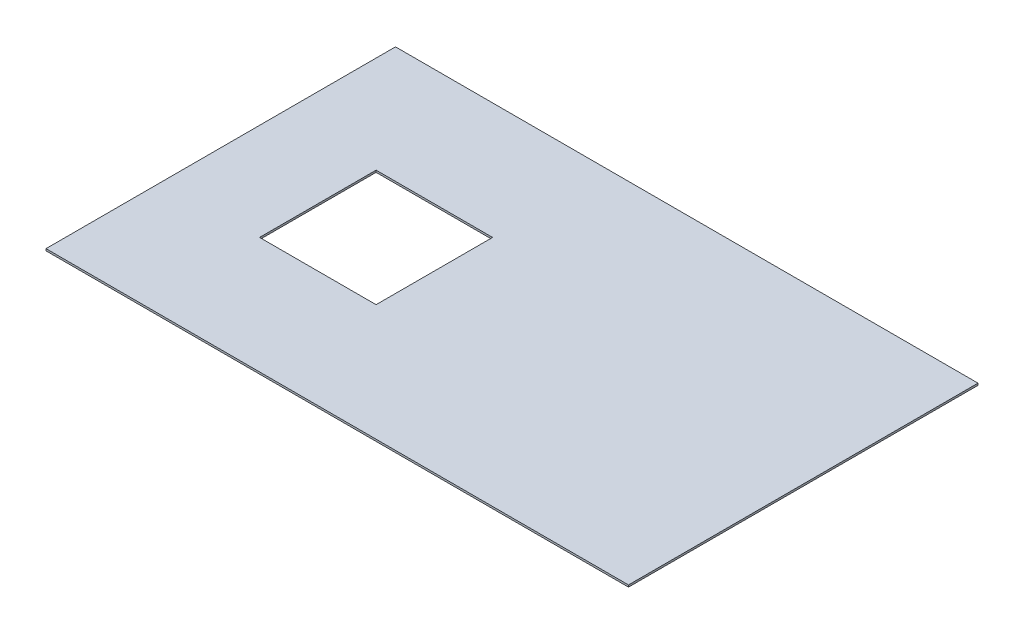
SolidWorks part; units mm, degrees
ref_plane "Front Plane" through (0, 0, 0) normal (0, 0, 1) x (1, 0, 0)
ref_plane "Top Plane" through (0, 0, 0) normal (0, 1, 0) x (1, 0, 0)
ref_plane "Right Plane" through (0, 0, 0) normal (1, 0, 0) x (0, 0, -1)
sketch "Sketch1" plane through (0, 0, 0) normal (0, 1, 0) x (1, 0, 0)
  line L1 (0, 0) -> (-3000, 0)
  line L2 (0, 0) -> (0, 1800)
  line L3 (0, 1800) -> (-3000, 1800)
  line L4 (-3000, 0) -> (-3000, 1800)
  dimension "D1" = 3000
  dimension "D2" = 1800
extrude "Extrude2" add sketch "Sketch1" along normal blind 10
sketch "Sketch2" plane through (0, 10, 0) normal (0, 1, 0) x (-1, 0, 0)
  line L1 (1900, -600) -> (2500, -600)
  line L2 (1900, -600) -> (1900, -1200)
  line L3 (1900, -1200) -> (2500, -1200)
  line L4 (2500, -600) -> (2500, -1200)
  line L5 (3000, 0) -> (0, 0) construction
  line L7 (3000, -1800) -> (3000, 0) construction
  dimension "D1" = 600
  dimension "D2" = 600
  dimension "D3" = 600
  dimension "D4" = 500
extrude "Cut-Extrude1" cut sketch "Sketch2" against normal blind 10
